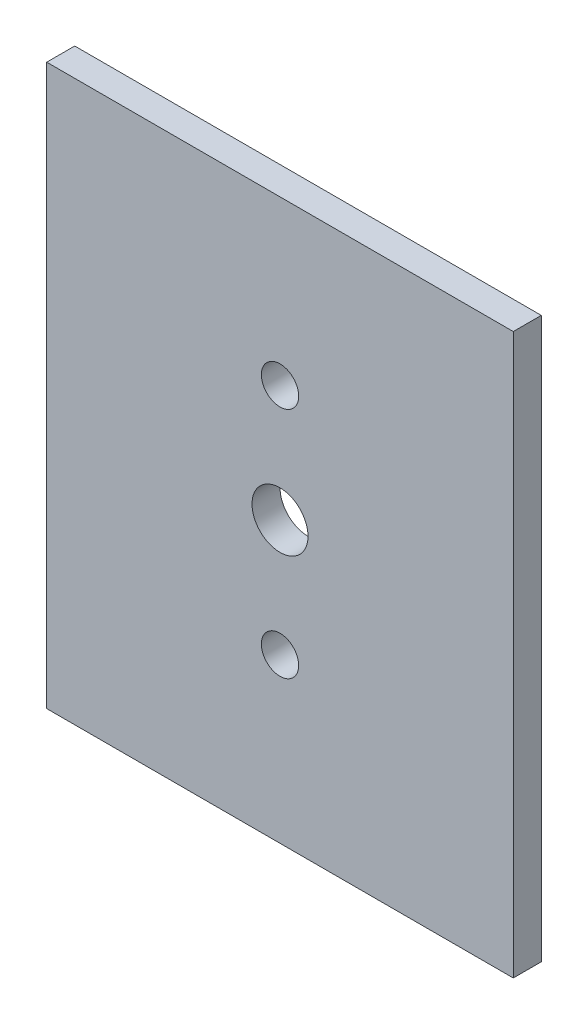
SolidWorks part; units mm, degrees
material "Plain Carbon Steel"
ref_plane "Front Plane" through (0, 0, 0) normal (0, 0, 1) x (1, 0, 0)
ref_plane "Top Plane" through (0, 0, 0) normal (0, 1, 0) x (1, 0, 0)
ref_plane "Right Plane" through (0, 0, 0) normal (1, 0, 0) x (0, 0, -1)
sketch "Sketch1" plane through (0, 0, 0) normal (0, 0, 1) x (1, 0, 0)
  line L1 (-25, -30) -> (25, -30)
  line L2 (-25, -30) -> (-25, 30)
  line L3 (-25, 30) -> (25, 30)
  line L4 (25, -30) -> (25, 30)
  line L5 (-25, -30) -> (25, 30) construction
  line L6 (-25, 30) -> (25, -30) construction
  circle A0 centre (0, 0) radius 3
  point P0 (0, 0)
  dimension "D3" = 6
  dimension "D1" = 50
  dimension "D2" = 60
extrude "Boss-Extrude1" add sketch "Sketch1" along normal blind 3
sketch "Sketch2" plane through (0, 0, 0) normal (0, 0, -1) x (-1, 0, 0)
  circle A0 centre (0, 12.5) radius 2
  circle A1 centre (0, 0) radius 3 construction
  circle A2 centre (0, -12.5) radius 2
  point P9 (0, 0)
  dimension "D1" = 4
  dimension "D2" = 12.5
  dimension "D3" = 2
extrude "Cut-Extrude1" cut sketch "Sketch2" against normal through all
